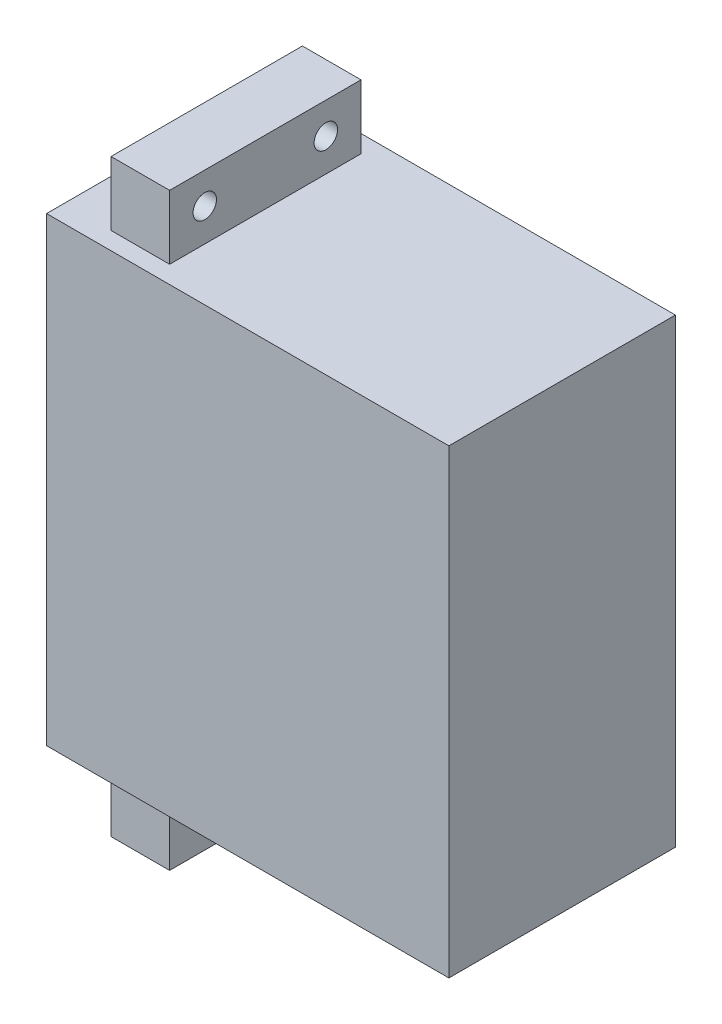
SolidWorks part; units mm, degrees
other "Markup1"
sketch "Sketch9" plane through (-2, -8.2, 0) normal (-0.9728, -0.1977, -0.1209) x (-0.1356, 0.0627, 0.9888)
ref_plane "Front Plane" through (0, 0, 0) normal (0, 0, 1) x (1, 0, 0)
ref_plane "Top Plane" through (0, 0, 0) normal (0, 1, 0) x (1, 0, 0)
ref_plane "Right Plane" through (0, 0, 0) normal (1, 0, 0) x (0, 0, -1)
sketch "Sketch1" plane through (0, 0, 0) normal (0, 0, 1) x (1, 0, 0)
  line L1 (0, 0) -> (51.5, 0)
  line L2 (0, 0) -> (0, 59)
  line L3 (0, 59) -> (51.5, 59)
  line L4 (51.5, 0) -> (51.5, 59)
  dimension "D1" = 59
  dimension "D2" = 51.5
extrude "Boss-Extrude1" add sketch "Sketch1" along normal blind 29
sketch "Sketch2" plane through (0, 59, 0) normal (0, 1, 0) x (1, 0, 0)
  line L0 (51.5, -29) -> (51.5, 0) construction
  line L1 (6, -2.25) -> (13.5, -2.25)
  line L2 (6, -2.25) -> (6, -26.75)
  line L3 (6, -26.75) -> (13.5, -26.75)
  line L4 (13.5, -2.25) -> (13.5, -26.75)
  dimension "D1" = 38
  dimension "D2" = 7.5
  dimension "D3" = 2.25
  dimension "D4" = 24.5
extrude "Boss-Extrude3" add sketch "Sketch2" along normal blind 8.2
ref_plane "Plane1" through (0, 29.5, 0) normal (0, 1, 0) x (1, 0, 0)
sketch "Sketch7" plane through (6, 0, 0) normal (-1, 0, 0) x (0, 0, 1)
  line L0 (14.5, 67.2) -> (14.5, 60.4723) construction
  line L1 (2.25, 67.2) -> (26.75, 67.2) construction
  line L2 (2.25, 67.2) -> (2.25, 59) construction
  circle A0 centre (6.75, 63.2) radius 1.5
  circle A1 centre (22.25, 63.2) radius 1.5
  dimension "D1" = 3
  dimension "D2" = 4
  dimension "D3" = 4.5
extrude "Cut-Extrude1" cut sketch "Sketch7" against normal blind 8.2
mirror "Mirror3" about plane through (0, 29.5, 0) normal (0, 1, 0) of "Cut-Extrude1", "Boss-Extrude3"
sketch "Sketch8" plane through (0, 0, 0) normal (-1, 0, 0) x (0, 0, 1)
  line L1 (2.25, 67.2) -> (26.75, 67.2) construction
  line L2 (0, 59) -> (0, 0) construction
  circle A0 centre (14.5, 43.7) radius 1.5
  dimension "D1" = 3
  dimension "D2" = 23.5
  dimension "D3" = 14.5
extrude "Boss-Extrude4" add sketch "Sketch8" along normal blind 2
